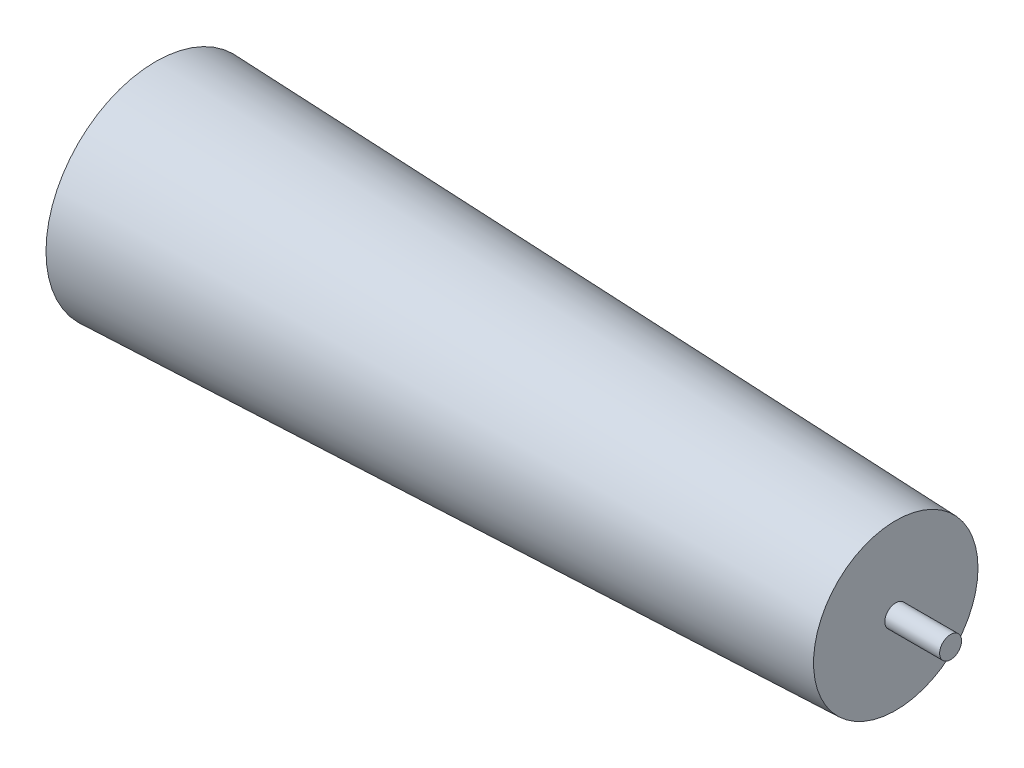
SolidWorks part; units mm, degrees
ref_plane "Front Plane" through (0, 0, 0) normal (0, 0, 1) x (1, 0, 0)
ref_plane "Top Plane" through (0, 0, 0) normal (0, 1, 0) x (1, 0, 0)
ref_plane "Right Plane" through (0, 0, 0) normal (1, 0, 0) x (0, 0, -1)
sketch "Sketch1" plane through (0, 0, 0) normal (1, 0, 0) x (0, 0, -1)
  circle A0 centre (0, 0) radius 40
  dimension "D1" = 80
ref_plane "Plane1" through (270, 0, 0) normal (1, 0, 0) x (0, 0, -1)
sketch "Sketch2" plane through (270, 0, 0) normal (1, 0, 0) x (0, 0, -1)
  circle A0 centre (0, 0) radius 30
  dimension "D1" = 60
loft "Loft1" add profiles "Sketch1", "Sketch2"
sketch "Sketch3" plane through (270, 0, 0) normal (1, 0, 0) x (0, 0, -1)
  circle A0 centre (0, 0) radius 4
  dimension "D1" = 8
extrude "Boss-Extrude1" add sketch "Sketch3" along normal blind 20 and the other way blind 280
